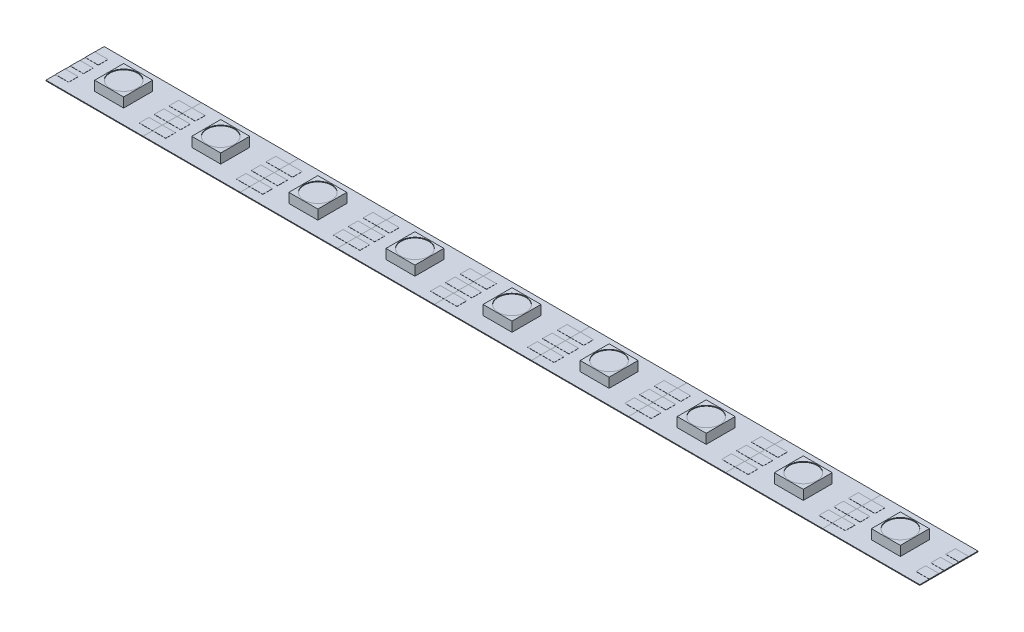
SolidWorks part; units mm, degrees
ref_plane "Front Plane" through (0, 0, 0) normal (0, 0, 1) x (1, 0, 0)
ref_plane "Top Plane" through (0, 0, 0) normal (0, 1, 0) x (1, 0, 0)
ref_plane "Right Plane" through (0, 0, 0) normal (1, 0, 0) x (0, 0, -1)
sketch "Sketch1" plane through (0, 0, 0) normal (0, 1, 0) x (1, 0, 0)
  line L0 (-8.3058, 4.9784) -> (8.3058, -4.9784) construction
  line L1 (-8.3058, 4.9784) -> (8.3058, 4.9784)
  line L2 (-8.3058, 4.9784) -> (-8.3058, -4.9784)
  line L3 (-8.3058, -4.9784) -> (8.3058, -4.9784)
  line L4 (8.3058, 4.9784) -> (8.3058, -4.9784)
  dimension "D1" = 9.9568
  dimension "D2" = 16.6116
extrude "Boss-Extrude1" add sketch "Sketch1" along normal blind 0.127
sketch "Sketch3" plane through (0, 0.127, 0) normal (0, 1, 0) x (1, 0, 0)
  line L0 (-8.3058, 4.9784) -> (8.3058, -4.9784) construction
  line L1 (-2.4765, 2.4765) -> (2.4765, -2.4765) construction
  line L2 (-2.4765, 2.4765) -> (2.4765, 2.4765)
  line L3 (-2.4765, 2.4765) -> (-2.4765, -2.4765)
  line L4 (-2.4765, -2.4765) -> (2.4765, -2.4765)
  line L5 (2.4765, 2.4765) -> (2.4765, -2.4765)
  dimension "D1" = 4.953
extrude "Boss-Extrude3" add sketch "Sketch3" along normal blind 1.651
sketch "Sketch4" plane through (0, 0.127, 0) normal (0, 1, 0) x (1, 0, 0)
  line L0 (-8.3058, 0) -> (8.3058, 0) construction
  line L1 (-8.3058, 4.9784) -> (-8.3058, -4.9784) construction
  line L2 (8.3058, -4.9784) -> (8.3058, 4.9784) construction
  line L3 (-6.047, 0) -> (-8.3058, 0) construction
  line L4 (-8.3058, 0.8255) -> (-6.047, 0.8255)
  line L5 (-8.3058, 0.8255) -> (-8.3058, -0.8255)
  line L6 (-8.3058, -0.8255) -> (-6.047, -0.8255)
  line L7 (-6.047, 0.8255) -> (-6.047, -0.8255)
  line L8 (-8.3058, 3.3655) -> (-6.047, 3.3655)
  line L9 (-6.047, 3.3655) -> (-6.047, 1.7145)
  line L10 (-8.3058, 1.7145) -> (-6.047, 1.7145)
  line L11 (-8.3058, 3.3655) -> (-8.3058, 1.7145)
  line L12 (-6.047, -3.3655) -> (-6.047, -1.7145)
  line L13 (-8.3058, -1.7145) -> (-6.047, -1.7145)
  line L14 (-8.3058, -3.3655) -> (-8.3058, -1.7145)
  line L15 (-8.3058, -3.3655) -> (-6.047, -3.3655)
  line L16 (0, 0) -> (0, -4.9784) construction
  line L17 (-8.3058, -4.9784) -> (8.3058, -4.9784) construction
  line L18 (8.3058, -3.3655) -> (8.3058, -1.7145)
  line L19 (8.3058, -3.3655) -> (6.047, -3.3655)
  line L20 (6.047, -3.3655) -> (6.047, -1.7145)
  line L21 (8.3058, -1.7145) -> (6.047, -1.7145)
  line L22 (8.3058, 0.8255) -> (8.3058, -0.8255)
  line L23 (8.3058, -0.8255) -> (6.047, -0.8255)
  line L24 (6.047, 0.8255) -> (6.047, -0.8255)
  line L25 (8.3058, 0.8255) -> (6.047, 0.8255)
  line L26 (8.3058, 1.7145) -> (6.047, 1.7145)
  line L27 (6.047, 3.3655) -> (6.047, 1.7145)
  line L28 (8.3058, 3.3655) -> (8.3058, 1.7145)
  line L29 (8.3058, 3.3655) -> (6.047, 3.3655)
  dimension "D1" = 1.651
  dimension "D2" = 2
extrude "Boss-Extrude4" add sketch "Sketch4" along normal blind 0.0254
sketch "Sketch5" plane through (0, 1.778, 0) normal (0, 1, 0) x (1, 0, 0)
  circle A0 centre (0, 0) radius 2.3483
extrude "Cut-Extrude1" cut sketch "Sketch5" against normal blind 0.127
pattern_linear "LPattern1" count 9 spacing 16.6116 along (1, 0, 0) of "Boss-Extrude3", "Boss-Extrude4", "Cut-Extrude1", "Boss-Extrude1"
